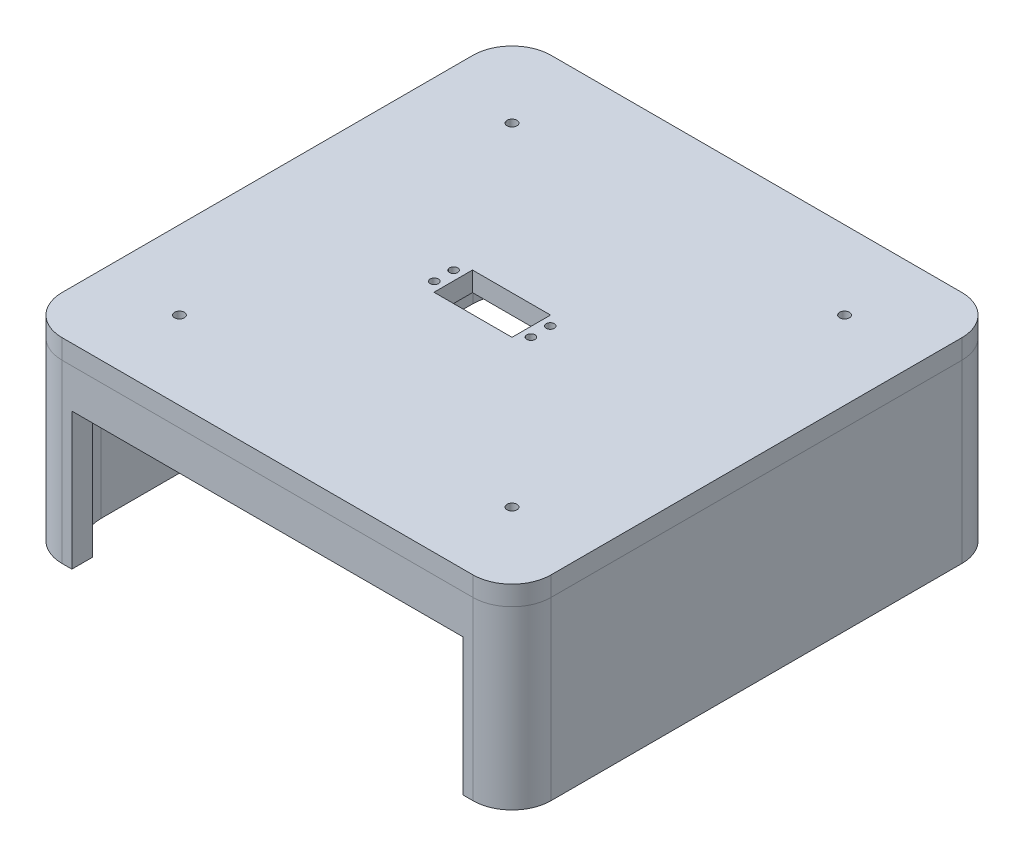
SolidWorks part; units mm, degrees
ref_plane "Front Plane" through (0, 0, 0) normal (0, 0, 1) x (1, 0, 0)
ref_plane "Top Plane" through (0, 0, 0) normal (0, 1, 0) x (1, 0, 0)
ref_plane "Right Plane" through (0, 0, 0) normal (1, 0, 0) x (0, 0, -1)
sketch "Sketch1" plane through (0, 0, 0) normal (0, 1, 0) x (1, 0, 0)
  line L1 (-125, -125) -> (125, -125)
  line L2 (-125, -125) -> (-125, 125)
  line L3 (-125, 125) -> (125, 125)
  line L4 (125, -125) -> (125, 125)
  line L5 (-115, -115) -> (115, -115)
  line L6 (-115, -115) -> (-115, 115)
  line L7 (-115, 115) -> (115, 115)
  line L8 (115, -115) -> (115, 115)
  line L9 (-115, -115) -> (115, 115) construction
  line L10 (-115, 115) -> (115, -115) construction
  point P0 (0, 0)
  point P6 (125, 0)
  point P7 (0, -125)
  point P8 (0, 0)
  dimension "D1" = 250
  dimension "D2" = 250
  dimension "D3" = 230
  dimension "D4" = 230
extrude "Boss-Extrude1" add sketch "Sketch1" along normal blind 90
sketch "Sketch2" plane through (0, 0, 125) normal (0, 0, 1) x (1, 0, 0)
  line L0 (-125, 0) -> (125, 0) construction
  line L1 (-100, 70) -> (100, 70)
  line L2 (-100, 70) -> (-100, 0)
  line L3 (-100, 0) -> (100, 0)
  line L4 (100, 70) -> (100, 0)
  line L6 (-125, 90) -> (125, 90) construction
  point P6 (0, 70)
  dimension "D1" = 200
  dimension "D2" = 20
extrude "Cut-Extrude1" cut sketch "Sketch2" against normal blind 50
fillet "Fillet1" radius 20 8 edges at (-115, 45, 115) (115, 45, 115) (115, 45, -115) (-115, 45, -115) (-125, 45, 125) (125, 45, 125) (125, 45, -125) (-125, 45, -125)
sketch "Sketch3" plane through (0, 90, 0) normal (0, 1, 0) x (1, 0, 0)
  line L1 (-105, -125) -> (105, -125)
  line L2 (-125, -105) -> (-125, 105)
  line L3 (-105, 125) -> (105, 125)
  line L4 (125, -105) -> (125, 105)
  line L5 (-125, -125) -> (125, 125) construction
  line L6 (-125, 125) -> (125, -125) construction
  arc A0 (-105, -125) -> (-125, -105) centre (-105, -105) cw
  arc A1 (105, -125) -> (125, -105) centre (105, -105) ccw
  arc A2 (105, 125) -> (125, 105) centre (105, 105) cw
  arc A3 (-125, 105) -> (-105, 125) centre (-105, 105) cw
  point P0 (0, 0)
  dimension "D3" = 20
  dimension "D1" = 250
  dimension "D2" = 250
extrude "Boss-Extrude2" add sketch "Sketch3" along normal blind 10 separate body
sketch "Sketch4" plane through (0, 100, 0) normal (0, 1, 0) x (1, 0, 0)
  line L0 (-125, 105) -> (-125, -105) construction
  line L1 (105, 125) -> (-105, 125) construction
  circle A0 centre (-85, 85) radius 2.5
  dimension "D1" = 5
  dimension "D2" = 40
  dimension "D3" = 40
extrude "Cut-Extrude2" cut sketch "Sketch4" against normal blind 10
pattern_linear "LPattern1" count 2 spacing 170 along (1, 0, 0) count 2 spacing 170 along (0, 0, 1) of "Cut-Extrude2"
sketch "Sketch5" plane through (0, 100, 0) normal (0, 1, 0) x (1, 0, 0)
  circle A0 centre (0, 0) radius 4.3133
sketch "Sketch6" plane through (0, 100, 0) normal (0, 1, 0) x (1, 0, 0)
  line L1 (-30.05, 9.85) -> (9.85, 9.85)
  line L2 (-30.05, 9.85) -> (-30.05, -9.85)
  line L3 (-30.05, -9.85) -> (9.85, -9.85)
  line L4 (9.85, 9.85) -> (9.85, -9.85)
  circle A0 centre (-34.8111, 4.925) radius 2.1
  circle A1 centre (-34.8111, -4.925) radius 2.1
  circle A2 centre (14.6111, -4.925) radius 2.1
  circle A3 centre (14.6111, 4.925) radius 2.1
extrude "Cut-Extrude3" cut sketch "Sketch6" against normal blind 10
